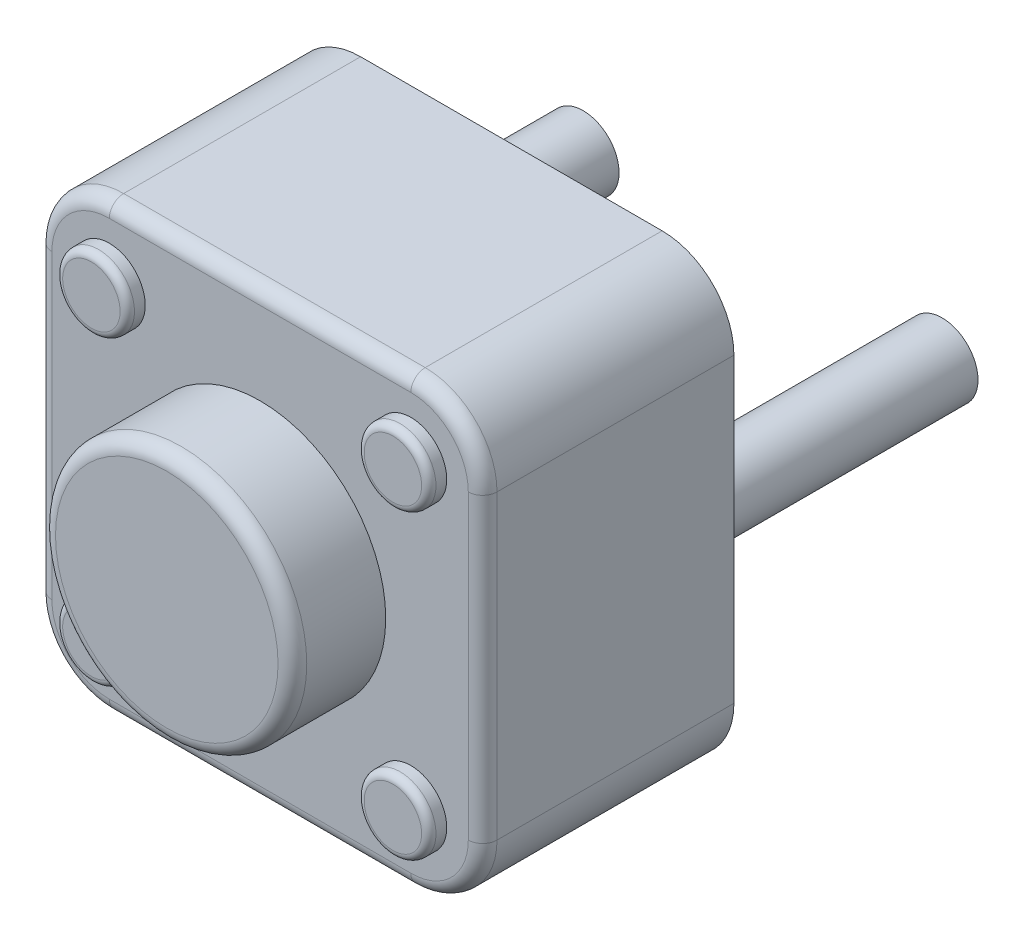
SolidWorks part; units mm, degrees
ref_plane "Front Plane" through (0, 0, 0) normal (0, 0, 1) x (1, 0, 0)
ref_plane "Top Plane" through (0, 0, 0) normal (0, 1, 0) x (1, 0, 0)
ref_plane "Right Plane" through (0, 0, 0) normal (1, 0, 0) x (0, 0, -1)
ref_plane "Plane1" through (0, 0, 3.5) normal (0, 0, 1) x (1, 0, 0)
sketch "Sketch1" plane through (0, 0, 3.5) normal (0, 0, 1) x (1, 0, 0)
  line L0 (3.1, 3.1) -> (-3.1, 3.1)
  line L1 (-3.1, 3.1) -> (-3.1, -3.1)
  line L2 (-3.1, -3.1) -> (3.1, -3.1)
  line L3 (3.1, -3.1) -> (3.1, 3.1)
extrude "Boss-Extrude1" add sketch "Sketch1" against normal blind 3.5
sketch "Sketch2" plane through (0, 0, 0) normal (0, 1, 0) x (1, 0, 0)
  line L0 (3, 3.5) -> (2.5, 3.5)
  line L1 (2.5, 3.5) -> (2.5, 0)
  line L2 (2.5, 0) -> (3, 0)
  line L3 (3, 0) -> (3, 3.5)
  line L4 (2.5, 3.5) -> (2.5, 0) construction
revolve "Revolve1" add sketch "Sketch2" angle 360 about L4
sketch "Sketch3" plane through (0, 0, 0) normal (0, 1, 0) x (1, 0, 0)
  line L0 (-2, 3.5) -> (-2.5, 3.5)
  line L1 (-2.5, 3.5) -> (-2.5, 0)
  line L2 (-2.5, 0) -> (-2, 0)
  line L3 (-2, 0) -> (-2, 3.5)
  line L4 (-2.5, 3.5) -> (-2.5, 0) construction
revolve "Revolve2" add sketch "Sketch3" angle 360 about L4
ref_plane "Plane2" through (0, -2.1, 0) normal (0, -1, 0) x (1, 0, 0)
sketch "Sketch4" plane through (0, -2.1, 0) normal (0, -1, 0) x (1, 0, 0)
  line L0 (2.6, 3.75) -> (2.1, 3.75)
  line L1 (2.1, 3.75) -> (2.1, 3.5)
  line L2 (2.1, 3.5) -> (2.6, 3.5)
  line L3 (2.6, 3.5) -> (2.6, 3.75)
  line L4 (2.1, 3.75) -> (2.1, 3.5) construction
revolve "Revolve3" add sketch "Sketch4" angle 360 about L4
ref_plane "Plane3" through (0, 2.1, 0) normal (0, -1, 0) x (1, 0, 0)
sketch "Sketch5" plane through (0, 2.1, 0) normal (0, -1, 0) x (1, 0, 0)
  line L0 (2.6, 3.75) -> (2.1, 3.75)
  line L1 (2.1, 3.75) -> (2.1, 3.5)
  line L2 (2.1, 3.5) -> (2.6, 3.5)
  line L3 (2.6, 3.5) -> (2.6, 3.75)
  line L4 (2.1, 3.75) -> (2.1, 3.5) construction
revolve "Revolve4" add sketch "Sketch5" angle 360 about L4
sketch "Sketch6" plane through (0, 2.1, 0) normal (0, -1, 0) x (1, 0, 0)
  line L0 (-1.6, 3.75) -> (-2.1, 3.75)
  line L1 (-2.1, 3.75) -> (-2.1, 3.5)
  line L2 (-2.1, 3.5) -> (-1.6, 3.5)
  line L3 (-1.6, 3.5) -> (-1.6, 3.75)
  line L4 (-2.1, 3.75) -> (-2.1, 3.5) construction
revolve "Revolve5" add sketch "Sketch6" angle 360 about L4
ref_plane "Plane4" through (0, 0, 0) normal (0, -1, 0) x (1, 0, 0)
sketch "Sketch7" plane through (0, 0, 0) normal (0, -1, 0) x (1, 0, 0)
  line L0 (1.75, 4.8) -> (0, 4.8)
  line L1 (0, 4.8) -> (0, 3.5)
  line L2 (0, 3.5) -> (1.75, 3.5)
  line L3 (1.75, 3.5) -> (1.75, 4.8)
  line L4 (0, 4.8) -> (0, 3.5) construction
revolve "Revolve6" add sketch "Sketch7" angle 360 about L4
sketch "Sketch8" plane through (0, -2.1, 0) normal (0, -1, 0) x (1, 0, 0)
  line L0 (-1.6, 3.75) -> (-2.1, 3.75)
  line L1 (-2.1, 3.75) -> (-2.1, 3.5)
  line L2 (-2.1, 3.5) -> (-1.6, 3.5)
  line L3 (-1.6, 3.5) -> (-1.6, 3.75)
  line L4 (-2.1, 3.75) -> (-2.1, 3.5) construction
revolve "Revolve7" add sketch "Sketch8" angle 360 about L4
fillet "Fillet1" radius 1 4 edges at (3.1, -3.1, 1.75) (3.1, 3.1, 1.75) (-3.1, 3.1, 1.75) (-3.1, -3.1, 1.75)
fillet "Fillet2" radius 0.1 4 edges at (-2.6, -2.1, 3.75) (1.6, 2.1, 3.75) (-2.6, 2.1, 3.75) (1.6, -2.1, 3.75)
fillet "Fillet3" radius 0.2 9 edges at (0, -3.1, 3.5) (-2.8071, -2.8071, 3.5) (2.8071, -2.8071, 3.5) (-3.1, 0, 3.5) (3.1, 0, 3.5) (-2.8071, 2.8071, 3.5) (2.8071, 2.8071, 3.5) (0, 3.1, 3.5) (-1.75, 0, 4.8)
